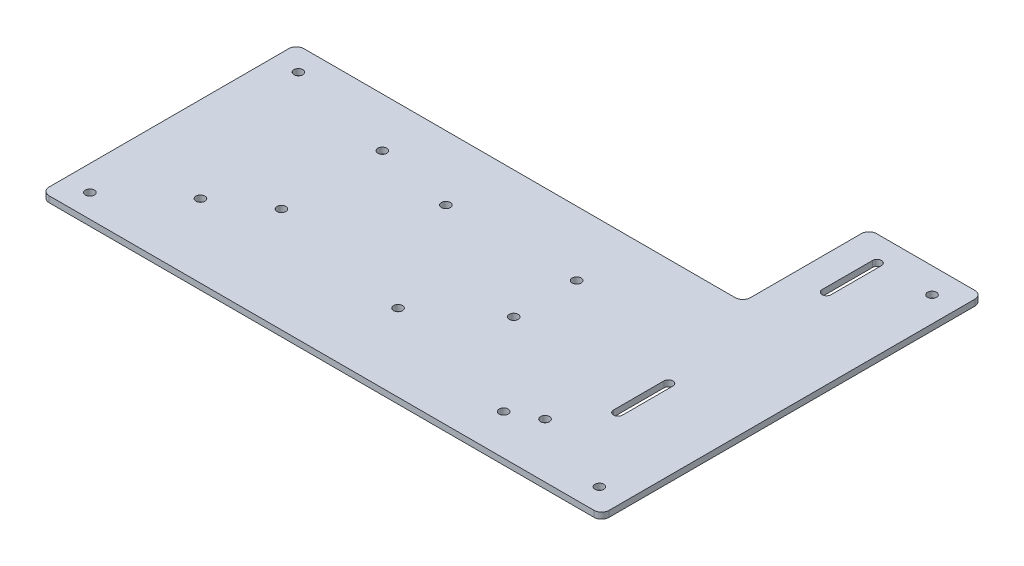
SolidWorks part; units mm, degrees
ref_plane "Front Plane" through (0, 0, 0) normal (0, 0, 1) x (1, 0, 0)
ref_plane "Top Plane" through (0, 0, 0) normal (0, 1, 0) x (1, 0, 0)
ref_plane "Right Plane" through (0, 0, 0) normal (1, 0, 0) x (0, 0, -1)
sketch "Sketch1" plane through (0, 0, 0) normal (0, 1, 0) x (1, 0, 0)
  line L1 (0, 0) -> (281.94, 0)
  line L2 (0, 0) -> (0, 128.27)
  line L3 (0, 128.27) -> (224.79, 128.27)
  line L4 (281.94, 0) -> (281.94, 191.77)
  line L5 (281.94, 191.77) -> (224.79, 191.77)
  line L6 (224.79, 191.77) -> (224.79, 128.27)
  dimension "D1" = 281.94
  dimension "D2" = 128.27
  dimension "D3" = 63.5
  dimension "D4" = 57.15
extrude "Boss-Extrude1" add sketch "Sketch1" along normal blind 3.0734
hole_wizard "Compressor Mounts" positions "Sketch2" profile "Sketch3" hole size "#8" standard "ANSI Inch" end condition through all
sketch "Sketch2" plane through (0, 3.0734, 0) normal (0, 1, 0) x (1, 0, 0)
  line L0 (102.6525, 76.835) -> (178.6525, 76.835) construction
  line L3 (140.6525, 76.835) -> (173.5615, 95.835) construction
  line L6 (140.6525, 76.835) -> (107.7435, 95.835) construction
  line L9 (140.6525, 76.835) -> (140.6525, 38.835) construction
  line L15 (-4.039, 64.135) -> (285.1472, 64.135) construction
  line L17 (0, 128.27) -> (0, 0) construction
  circle A0 centre (140.6525, 76.835) radius 38 construction
  point P0 (140.6525, 38.835)
  point P2 (107.7435, 95.835)
  point P4 (173.5615, 95.835)
  point P47 (0, 64.135)
  dimension "D1" = 76
  dimension "D2" = 30
  dimension "D3" = 120
  dimension "D4" = 120
  dimension "D5" = 140.6525
  dimension "D6" = 12.7
sketch "Sketch3" plane through (140.6525, 3.0734, -38.835) normal (1, 0, 0) x (0, 0, 1)
  line L0 (0, 0) -> (0, 3.0734)
  line L1 (0, 3.0734) -> (2.2479, 3.0734)
  line L2 (2.2479, 3.0734) -> (2.2479, 0)
  line L5 (2.2479, 0) -> (0, 0)
  line L11 (0, -6.35) -> (0, 107.95) construction
  dimension "Thru Hole Dia." = 4.4958
  dimension "Thru Hole Depth" = 3.0734
hole_wizard "#8 Clearance Hole2" positions "Sketch4" profile "Sketch5" hole size "#8" standard "ANSI Inch" end condition through all
sketch "Sketch4" plane through (0, 3.0734, 0) normal (0, 1, 0) x (1, 0, 0)
  line L0 (0, 128.27) -> (0, 0) construction
  line L4 (0, 64.135) -> (288.29, 64.135) construction
  line L15 (73.152, 96.6855) -> (73.152, 16.6605) construction
  line L20 (12.827, 96.6855) -> (12.827, 16.6605) construction
  line L21 (281.94, 191.77) -> (224.79, 191.77) construction
  line L22 (281.94, 0) -> (281.94, 191.77) construction
  line L23 (0, 0) -> (281.94, 0) construction
  circle A1 centre (140.6525, 76.835) radius 38 construction
  point P2 (12.7, 11.635)
  point P4 (269.24, 11.635)
  point P28 (269.24, 179.07)
  point P29 (12.7, 116.635)
  point P151 (173.5615, 64.135)
  point P154 (140.6525, 38.835)
  point P163 (107.7435, 95.835)
  point P166 (173.5615, 95.835)
  point P175 (212.344, 20.32)
  point P180 (68.072, 103.505)
  point P182 (68.072, 52.705)
  point P188 (43.18, 36.83)
  point P191 (226.06, 27.432)
  dimension "D8" = 60.325
  dimension "D5" = 69.596
  dimension "D4" = 12.7
  dimension "D1" = 12.7
  dimension "D2" = 52.5
  dimension "D3" = 12.7
  dimension "D6" = 20.32
  dimension "D7" = 12.827
  dimension "D9" = 5.08
  dimension "D10" = 50.8
  dimension "D11" = 11.43
  dimension "D12" = 36.83
  dimension "D13" = 43.18
  dimension "D14" = 27.432
  dimension "D15" = 55.88
sketch "Sketch5" plane through (12.7, 3.0734, -11.635) normal (1, 0, 0) x (0, 0, 1)
  line L0 (0, 0) -> (0, 3.0734)
  line L1 (0, 3.0734) -> (2.2479, 3.0734)
  line L2 (2.2479, 3.0734) -> (2.2479, 0)
  line L5 (2.2479, 0) -> (0, 0)
  line L11 (0, -6.35) -> (0, 107.95) construction
  dimension "Thru Hole Dia." = 4.4958
  dimension "Thru Hole Depth" = 3.0734
fillet "Fillet1" radius 3.81 6 edges at (281.94, 1.5367, 0) (0, 1.5367, -128.27) (0, 1.5367, 0) (281.94, 1.5367, -191.77) (224.79, 1.5367, -191.77) (224.79, 1.5367, -128.27)
sketch "Sketch7" plane through (0, 3.0734, 0) normal (0, 1, 0) x (1, 0, 0)
  line L0 (241.554, 179.07) -> (241.554, 153.67) construction
  line L1 (243.8019, 179.07) -> (243.8019, 153.67)
  line L2 (239.3061, 179.07) -> (239.3061, 153.67)
  line L3 (279.3963, 113.87) -> (210.4049, 113.87) construction
  line L4 (278.13, 191.77) -> (228.6, 191.77) construction
  line L5 (281.94, 3.81) -> (281.94, 187.96) construction
  line L6 (241.554, 48.67) -> (241.554, 74.07) construction
  line L7 (243.8019, 48.67) -> (243.8019, 74.07)
  line L8 (239.3061, 48.67) -> (239.3061, 74.07)
  arc A0 (243.8019, 179.07) -> (239.3061, 179.07) centre (241.554, 179.07) ccw
  arc A1 (239.3061, 153.67) -> (243.8019, 153.67) centre (241.554, 153.67) ccw
  arc A3 (243.8019, 48.67) -> (239.3061, 48.67) centre (241.554, 48.67) cw
  arc A4 (239.3061, 74.07) -> (243.8019, 74.07) centre (241.554, 74.07) cw
  point P2 (241.554, 166.37)
  point P15 (241.554, 61.37)
  dimension "D2" = 2.2479
  dimension "D1" = 52.5
  dimension "D3" = 25.4
  dimension "D4" = 12.7
  dimension "D5" = 40.386
extrude "Cut-Extrude1" cut sketch "Sketch7" against normal through all
